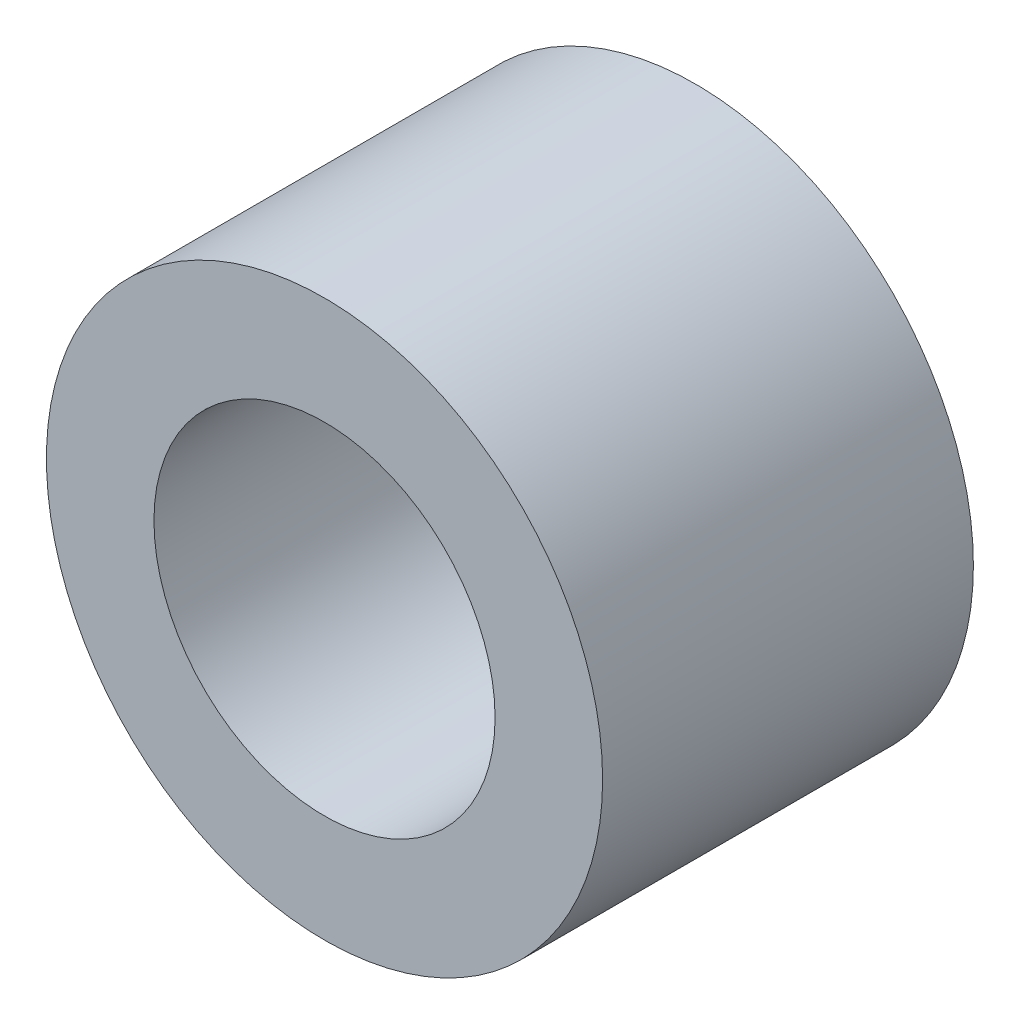
SolidWorks part; units mm, degrees
material "Nylon 6/10"
ref_plane "Front Plane" through (0, 0, 0) normal (0, 0, 1) x (1, 0, 0)
ref_plane "Top Plane" through (0, 0, 0) normal (0, 1, 0) x (1, 0, 0)
ref_plane "Right Plane" through (0, 0, 0) normal (1, 0, 0) x (0, 0, -1)
sketch "Sketch1" plane through (0, 0, 0) normal (0, 0, 1) x (1, 0, 0)
  circle A0 centre (0, 0) radius 2.3812
  circle A1 centre (0, 0) radius 1.4605
  dimension "OD" = 4.7625
  dimension "ID" = 2.921
extrude "Extrude1" add sketch "Sketch1" along normal mid plane 3.175
sketch "Sketch2" plane through (0, 0, 0) normal (1, 0, 0) x (0, 0, -1)
  line L0 (-1.5875, -1.4605) -> (1.5875, -1.4605) construction
  line L3 (1.5875, 1.4605) -> (-1.5875, 1.4605) construction
  line L5 (-1.5875, -1.4605) -> (1.5875, -1.4605)
  line L6 (1.5875, 1.4605) -> (-1.5875, 1.4605)
sketch "Sketch4" plane through (0, 0, 1.5875) normal (0, 0, 1) x (1, 0, 0)
  line L0 (0, 0) -> (-1.0327, 1.0327)
  line L1 (0, -55) -> (0, 55) construction
  circle A0 centre (0, 0) radius 1.4605 construction
  dimension "D1" = 45
